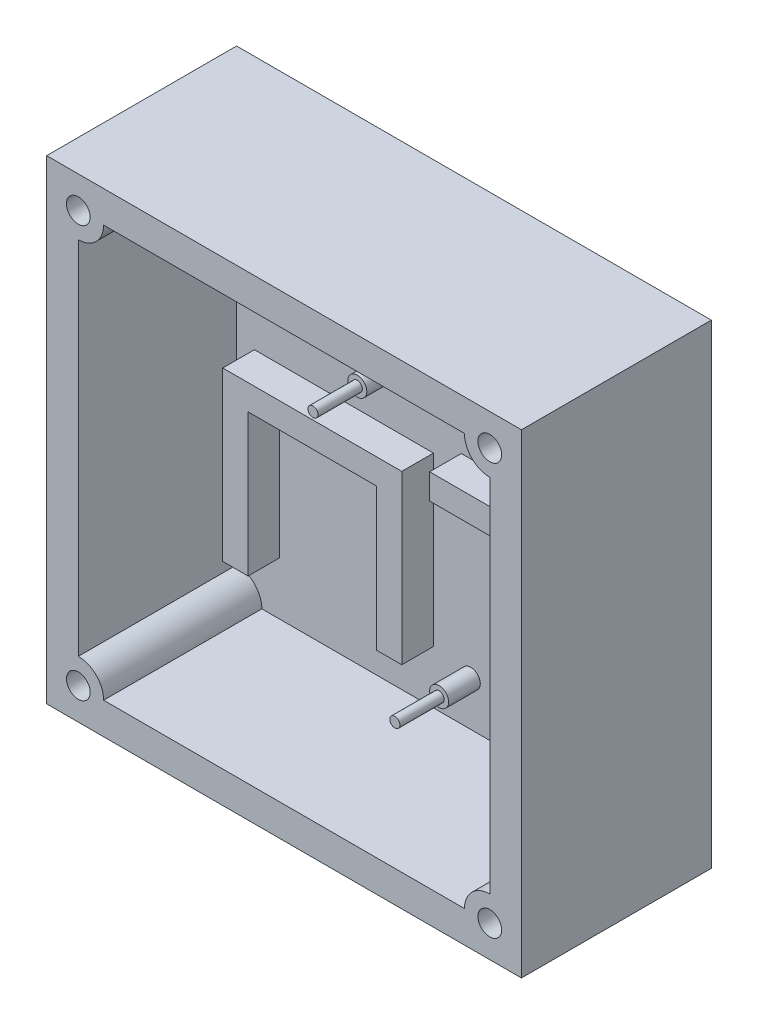
SolidWorks part; units mm, degrees
ref_plane "Front Plane" through (0, 0, 0) normal (0, 0, 1) x (1, 0, 0)
ref_plane "Top Plane" through (0, 0, 0) normal (0, 1, 0) x (1, 0, 0)
ref_plane "Right Plane" through (0, 0, 0) normal (1, 0, 0) x (0, 0, -1)
sketch "Sketch1" plane through (0, 0, 0) normal (0, 0, 1) x (1, 0, 0)
  line L1 (-47.625, -47.625) -> (47.625, -47.625)
  line L2 (-47.625, -47.625) -> (-47.625, 47.625)
  line L3 (-47.625, 47.625) -> (47.625, 47.625)
  line L4 (47.625, -47.625) -> (47.625, 47.625)
  line L5 (-47.625, -47.625) -> (47.625, 47.625) construction
  line L6 (-47.625, 47.625) -> (47.625, -47.625) construction
  point P0 (0, 0)
  dimension "D1" = 95.25
  dimension "D2" = 95.25
extrude "Boss-Extrude1" add sketch "Sketch1" along normal blind 38.1
shell "Shell1" thickness 6.35
ref_plane "Plane1" through (0, 0, 38.1) normal (0, 0, 1) x (1, 0, 0)
sketch "Sketch2" plane through (0, 0, 38.1) normal (0, 0, 1) x (1, 0, 0)
  line L0 (41.275, 41.275) -> (-41.275, 41.275) construction
  line L1 (-41.275, 41.275) -> (-41.275, -41.275) construction
  line L2 (-41.275, 41.275) -> (-36.195, 41.275)
  line L3 (-41.275, 41.275) -> (-41.275, 36.195)
  line L4 (41.275, 41.275) -> (-41.275, 41.275) construction
  line L5 (41.275, -41.275) -> (41.275, 41.275) construction
  line L6 (36.195, 41.275) -> (41.275, 41.275)
  line L7 (41.275, 41.275) -> (41.275, 36.195)
  line L8 (-41.275, -41.275) -> (41.275, -41.275) construction
  line L9 (41.275, -36.195) -> (41.275, -41.275)
  line L10 (41.275, -41.275) -> (36.195, -41.275)
  line L11 (-41.275, -41.275) -> (41.275, -41.275) construction
  line L12 (-41.275, -36.195) -> (-41.275, -41.275)
  line L13 (-41.275, -41.275) -> (-36.195, -41.275)
  arc A0 (-36.195, 41.275) -> (-41.275, 36.195) centre (-41.275, 41.275) cw
  arc A1 (36.195, 41.275) -> (41.275, 36.195) centre (41.275, 41.275) ccw
  arc A2 (41.275, -36.195) -> (36.195, -41.275) centre (41.275, -41.275) ccw
  arc A3 (-41.275, -36.195) -> (-36.195, -41.275) centre (-41.275, -41.275) cw
  dimension "D1" = 5.08
extrude "Boss-Extrude2" add sketch "Sketch2" against normal up to surface (31.75 mm away) up to face at (0, 0, 6.35)
sketch "Sketch3" plane through (0, 0, 6.35) normal (0, 0, 1) x (1, 0, 0)
  line L0 (41.275, -36.195) -> (41.275, 36.195) construction
  circle A0 centre (35.0157, 31.115) radius 1.905
  circle A1 centre (-10.7043, 31.115) radius 1.016
  circle A2 centre (-10.7043, 13.335) radius 1.905
  circle A3 centre (35.0157, 13.335) radius 1.905
  dimension "D1" = 3.81
  dimension "D2" = 2.032
  dimension "D3" = 6.2593
  dimension "D4" = 17.78
  dimension "D5" = 45.72
  dimension "D6" = 10.16
extrude "Boss-Extrude3" add sketch "Sketch3" along normal blind 6.35
ref_plane "Plane2" through (0, 0, 12.7) normal (0, 0, 1) x (1, 0, 0)
sketch "Sketch4" plane through (0, 0, 12.7) normal (0, 0, 1) x (1, 0, 0)
  circle A0 centre (-10.7043, 31.115) radius 1.016
  circle A1 centre (-10.7043, 13.335) radius 1.016
  circle A2 centre (35.0157, 31.115) radius 1.016
  circle A3 centre (35.0157, 13.335) radius 1.016
  dimension "D1" = 2.032
extrude "Boss-Extrude4" add sketch "Sketch4" along normal blind 8.89
ref_plane "Plane3" through (0, 0, 6.35) normal (0, 0, 1) x (1, 0, 0)
sketch "Sketch5" plane through (0, 0, 6.35) normal (0, 0, 1) x (1, 0, 0)
  line L0 (-36.195, -41.275) -> (36.195, -41.275) construction
  line L5 (3.81, 0.635) -> (3.81, -40.6427) construction
  line L6 (3.81, 0.635) -> (35.56, 0.635)
  line L7 (3.81, 0.635) -> (3.81, 5.715)
  line L8 (3.81, 5.715) -> (35.56, 5.715)
  line L9 (35.56, 0.635) -> (35.56, 5.715)
  line L10 (3.81, 0.635) -> (35.56, 5.715) construction
  line L11 (3.81, 5.715) -> (35.56, 0.635) construction
  line L12 (35.56, 0.635) -> (35.56, -28.5697) construction
  line L13 (41.275, -36.195) -> (41.275, 36.195) construction
  circle A0 centre (5.715, -32.385) radius 1.905
  circle A1 centre (33.655, -32.385) radius 1.905
  point P4 (19.685, 3.175)
  dimension "D4" = 3.81
  dimension "D1" = 8.89
  dimension "D2" = 33.02
  dimension "D3" = 27.94
  dimension "D5" = 5.08
  dimension "D6" = 7.62
extrude "Boss-Extrude5" add sketch "Sketch5" along normal blind 6.35
ref_plane "Plane4" through (0, 0, 12.7) normal (0, 0, 1) x (1, 0, 0)
sketch "Sketch7" plane through (0, 0, 12.7) normal (0, 0, 1) x (1, 0, 0)
  circle A0 centre (5.715, -32.385) radius 1.016
  circle A1 centre (33.655, -32.385) radius 1.016
  dimension "D1" = 2.032
extrude "Boss-Extrude6" add sketch "Sketch7" along normal blind 8.89
ref_plane "Plane5" through (0, 0, 38.1) normal (0, 0, 1) x (1, 0, 0)
sketch "Sketch8" plane through (0, 0, 38.1) normal (0, 0, 1) x (1, 0, 0)
  circle A0 centre (-41.275, 41.275) radius 2.3812
  circle A1 centre (41.275, 41.275) radius 2.3812
  circle A2 centre (41.275, -41.275) radius 2.3812
  circle A3 centre (-41.275, -41.275) radius 2.3812
  arc A4 (-36.195, -41.275) -> (-41.275, -36.195) centre (-41.275, -41.275) ccw construction
  arc A5 (-41.275, 36.195) -> (-36.195, 41.275) centre (-41.275, 41.275) ccw construction
  arc A6 (36.195, 41.275) -> (41.275, 36.195) centre (41.275, 41.275) ccw construction
  arc A7 (41.275, -36.195) -> (36.195, -41.275) centre (41.275, -41.275) ccw construction
  point P8 (0, 0)
  point P9 (0, 0)
  point P10 (0, 0)
  point P11 (0, 0)
  dimension "D1" = 4.7625
extrude "Cut-Extrude1" cut sketch "Sketch8" against normal blind 8.89
ref_plane "Plane7" through (0, 0, 6.35) normal (0, 0, 1) x (1, 0, 0)
sketch "Sketch10" plane through (0, 0, 6.35) normal (0, 0, 1) x (1, 0, 0)
  line L0 (-37.6969, -30.607) -> (-37.6969, 2.9972)
  line L1 (-37.6969, 2.9972) -> (-1.7813, 2.9972)
  line L2 (-1.7813, 2.9972) -> (-1.7813, -30.607)
  line L3 (-1.7813, -30.607) -> (-6.8613, -30.607)
  line L4 (-6.8613, -30.607) -> (-6.8613, -2.0828)
  line L5 (-6.8613, -2.0828) -> (-32.6169, -2.0828)
  line L6 (-32.6169, -2.0828) -> (-32.6169, -30.607)
  line L7 (-32.6169, -30.607) -> (-37.6969, -30.607)
  line L8 (-36.195, -41.275) -> (36.195, -41.275) construction
  line L9 (-41.275, 36.195) -> (-41.275, -36.195) construction
  dimension "D1" = 5.08
  dimension "D2" = 25.7556
  dimension "D3" = 28.5242
  dimension "D4" = 5.08
  dimension "D5" = 10.668
  dimension "D6" = 3.5781
extrude "Boss-Extrude7" add sketch "Sketch10" along normal blind 6.35
